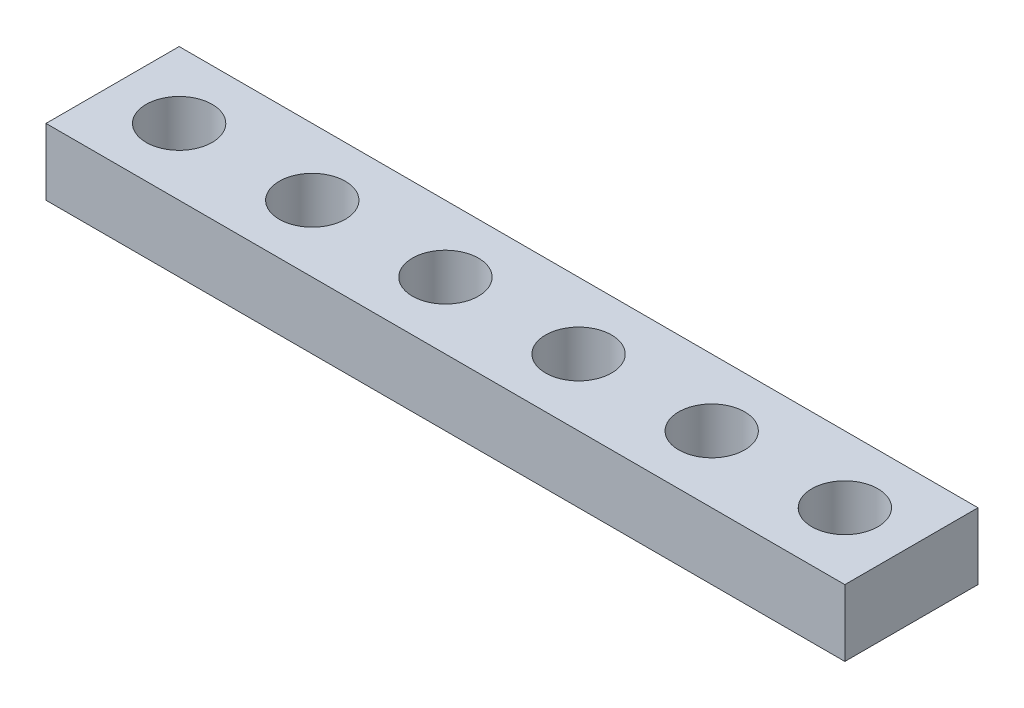
SolidWorks part; units mm, degrees
ref_plane "Front Plane" through (0, 0, 0) normal (0, 0, 1) x (1, 0, 0)
ref_plane "Top Plane" through (0, 0, 0) normal (0, 1, 0) x (1, 0, 0)
ref_plane "Right Plane" through (0, 0, 0) normal (1, 0, 0) x (0, 0, -1)
sketch "Sketch1" plane through (0, 0, 0) normal (0, 1, 0) x (1, 0, 0)
  line L1 (-19.05, 3.175) -> (19.05, 3.175)
  line L2 (-19.05, 3.175) -> (-19.05, -3.175)
  line L3 (-19.05, -3.175) -> (19.05, -3.175)
  line L4 (19.05, 3.175) -> (19.05, -3.175)
  line L5 (-19.05, 3.175) -> (19.05, -3.175) construction
  line L6 (-19.05, -3.175) -> (19.05, 3.175) construction
  point P0 (0, 0)
  dimension "D1" = 6.35
  dimension "D2" = 38.1
extrude "Boss-Extrude1" add sketch "Sketch1" along normal blind 3.175
sketch "Sketch2" plane through (0, 3.175, 0) normal (0, 1, 0) x (1, 0, 0)
  line L0 (19.05, -3.175) -> (19.05, 3.175) construction
  circle A0 centre (15.875, 0) radius 1.5748
  dimension "D1" = 3.1496
  dimension "D2" = 3.175
extrude "Cut-Extrude1" cut sketch "Sketch2" against normal through all
pattern_linear "LPattern1" count 6 spacing 6.35 along (-1, 0, 0) of "Cut-Extrude1"
